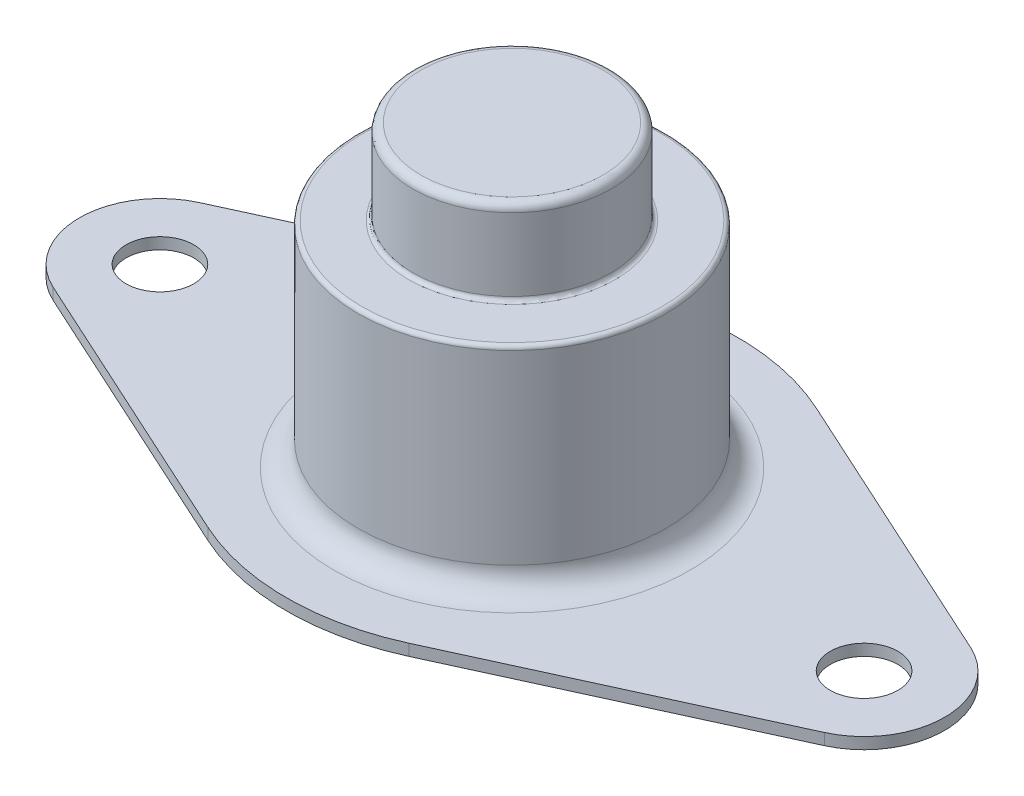
SolidWorks part; units mm, degrees
ref_plane "Front Plane" through (0, 0, 0) normal (0, 0, 1) x (1, 0, 0)
ref_plane "Top Plane" through (0, 0, 0) normal (0, 1, 0) x (1, 0, 0)
ref_plane "Right Plane" through (0, 0, 0) normal (1, 0, 0) x (0, 0, -1)
sketch "Sketch1" plane through (0, 0, 0) normal (0, 1, 0) x (1, 0, 0)
  line L0 (-23.9302, 4.5467) -> (-6.2407, 12.6401)
  line L1 (6.2407, 12.6401) -> (23.9302, 4.5467)
  line L2 (23.9302, -4.5467) -> (6.2407, -12.6401)
  line L3 (-6.2407, -12.6401) -> (-23.9302, -4.5467)
  line L4 (0, 1) -> (0, -1) construction
  line L5 (21.85, 0) -> (-21.85, 0) construction
  arc A0 (6.2407, 12.6401) -> (-6.2407, 12.6401) centre (0, -1) ccw
  arc A1 (-6.2407, -12.6401) -> (6.2407, -12.6401) centre (0, 1) ccw
  arc A2 (-23.9302, -4.5467) -> (-23.9302, 4.5467) centre (-21.85, 0) cw
  arc A3 (23.9302, 4.5467) -> (23.9302, -4.5467) centre (21.85, 0) cw
  dimension "D1" = 15
  dimension "D2" = 15
  dimension "D3" = 5
  dimension "D4" = 5
  dimension "D5" = 53.7
  dimension "D6" = 28
extrude "Boss-Extrude1" add sketch "Sketch1" along normal blind 0.71
sketch "Sketch4" plane through (0, 0, 0) normal (0, 1, 0) x (1, 0, 0)
  line L0 (21.85, 0) -> (-21.85, 0) construction
  line L1 (21.85, 0) -> (-21.85, 0) construction
  circle A1 centre (21.85, 0) radius 2.1
  dimension "D1" = 4.2
  dimension "D2" = 21.85
extrude "Cut-Extrude1" cut sketch "Sketch4" along normal through all
sketch "Sketch2" plane through (0, 0, 0) normal (0, 1, 0) x (1, 0, 0)
  circle A0 centre (0, 0) radius 9.55
  dimension "D1" = 19.1
extrude "Boss-Extrude2" add sketch "Sketch2" along normal blind 14
fillet "Fillet1" radius 1.5 1 edges at (0, 0.71, 9.55)
sketch "Sketch3" plane through (0, 14, 0) normal (0, 1, 0) x (1, 0, 0)
  circle A0 centre (0, 0) radius 6.15
  dimension "D1" = 12.3
extrude "Boss-Extrude3" add sketch "Sketch3" along normal blind 5.25
fillet "Fillet2" radius 0.25 2 edges at (0, 14, 9.55) (0, 14, 6.15)
fillet "Fillet3" radius 0.5 1 edges at (0, 19.25, 6.15)
mirror "Mirror1" about plane through (0, 0, 0) normal (1, 0, 0) of "Cut-Extrude1"
shell "Shell1" thickness 0.66
